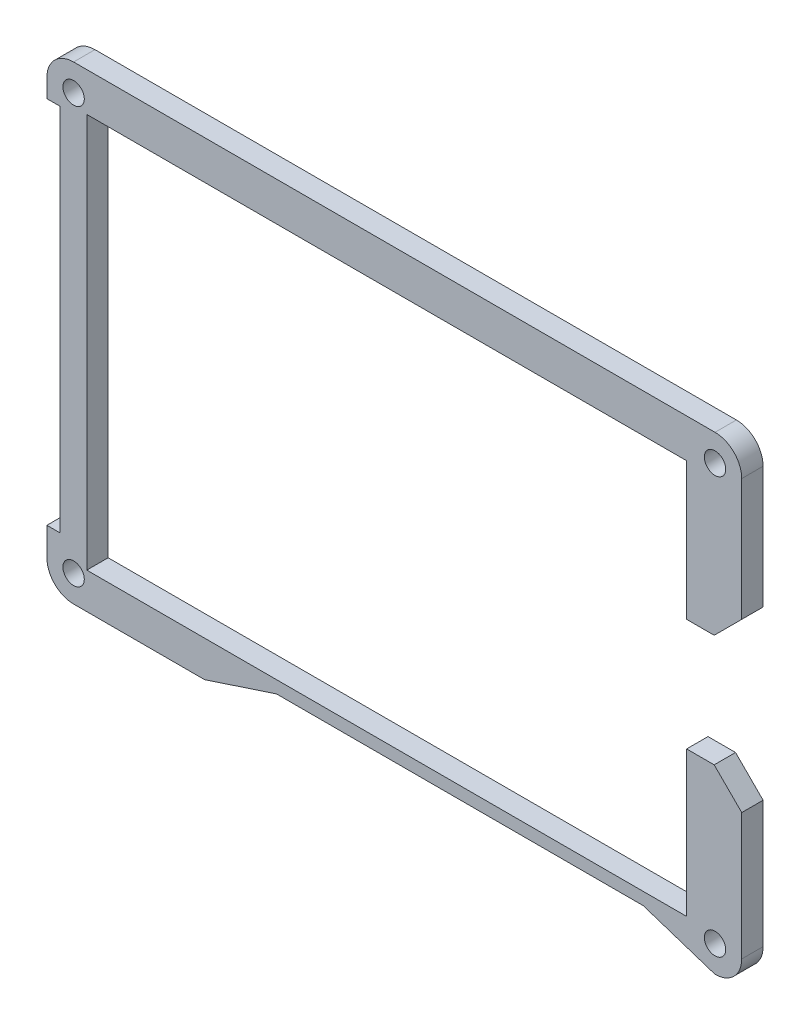
SolidWorks part; units mm, degrees
ref_plane "Front Plane" through (0, 0, 0) normal (0, 0, 1) x (1, 0, 0)
ref_plane "Top Plane" through (0, 0, 0) normal (0, 1, 0) x (1, 0, 0)
ref_plane "Right Plane" through (0, 0, 0) normal (1, 0, 0) x (0, 0, -1)
sketch "Sketch1" plane through (0, 0, 0) normal (0, 0, 1) x (1, 0, 0)
  line L0 (-401.0571, 148.341) -> (-380.1672, 148.341)
  line L1 (-399.1521, 148.341) -> (-399.1521, 95.6449)
  line L2 (-395.3675, 92.9525) -> (-395.3675, 149.2432)
  line L3 (-395.3675, 149.2432) -> (-309.8086, 149.2432)
  line L4 (-395.3675, 92.9525) -> (-309.8086, 92.9525)
  line L5 (-309.8086, 149.2432) -> (-309.8086, 92.9525)
  line L6 (-309.8086, 128.8851) -> (-321.2743, 128.8851)
  line L7 (-321.2743, 128.8851) -> (-321.2743, 115.6771)
  line L8 (-321.2743, 115.6771) -> (-309.8086, 115.6771)
  line L9 (-309.8086, 128.8851) -> (-305.8779, 128.8851)
  line L10 (-375.4172, 95.6449) -> (-401.0571, 95.6449)
  line L11 (-401.0571, 150.9566) -> (-401.0571, 148.341) construction
  line L12 (-305.7573, 154.7804) -> (-397.2471, 154.7804) construction
  line L13 (-301.9473, 91.6317) -> (-301.9473, 150.9704) construction
  line L14 (-315.9973, 91.1883) -> (-305.7573, 87.8217) construction
  line L15 (-315.9973, 91.1883) -> (-368.3165, 91.1883) construction
  line L16 (-368.3165, 91.1883) -> (-378.5565, 87.8217) construction
  line L17 (-378.5565, 87.8217) -> (-397.2472, 87.8217) construction
  line L18 (-401.0571, 95.6449) -> (-401.0571, 91.6593) construction
  line L19 (-401.0571, 150.9566) -> (-401.0571, 148.341)
  line L20 (-305.7573, 154.7804) -> (-397.2471, 154.7804)
  line L21 (-301.9473, 91.6317) -> (-301.9473, 150.9704)
  line L22 (-315.9973, 91.1883) -> (-305.7573, 87.8217)
  line L23 (-315.9973, 91.1883) -> (-368.3165, 91.1883)
  line L24 (-368.3165, 91.1883) -> (-378.5565, 87.8217)
  line L25 (-378.5565, 87.8217) -> (-397.2472, 87.8217)
  line L26 (-401.0571, 95.6449) -> (-401.0571, 91.6593)
  line L27 (-305.8779, 128.8851) -> (-301.9473, 132.8158)
  line L28 (-309.8086, 115.6771) -> (-305.8779, 115.6771)
  line L29 (-305.8779, 115.6771) -> (-301.9473, 111.7464)
  line L30 (-309.8086, 141.4927) -> (-301.9473, 141.4927) construction
  line L31 (-305.878, 141.4927) -> (-305.8779, 128.8851) construction
  arc A0 (-397.2471, 154.7804) -> (-401.0571, 150.9566) centre (-397.2471, 150.9704) ccw construction
  arc A1 (-301.9473, 150.9704) -> (-305.7573, 154.7804) centre (-305.7573, 150.9704) ccw construction
  arc A2 (-305.7573, 87.8217) -> (-301.9473, 91.6317) centre (-305.7573, 91.6317) ccw construction
  arc A3 (-401.0571, 91.6593) -> (-397.2472, 87.8217) centre (-397.2472, 91.6317) ccw construction
  arc A4 (-397.2471, 154.7804) -> (-401.0571, 150.9566) centre (-397.2471, 150.9704) ccw
  arc A5 (-301.9473, 150.9704) -> (-305.7573, 154.7804) centre (-305.7573, 150.9704) ccw
  arc A6 (-305.7573, 87.8217) -> (-301.9473, 91.6317) centre (-305.7573, 91.6317) ccw
  arc A7 (-401.0571, 91.6593) -> (-397.2472, 87.8217) centre (-397.2472, 91.6317) ccw
  circle A8 centre (-397.2471, 150.9704) radius 1.3462 construction
  circle A9 centre (-305.7573, 150.9704) radius 1.3462 construction
  circle A10 centre (-305.7573, 91.6317) radius 1.3462 construction
  circle A11 centre (-397.2472, 91.6317) radius 1.3462 construction
  circle A12 centre (-397.2471, 150.9704) radius 1.3462
  circle A13 centre (-305.7573, 150.9704) radius 1.3462
  circle A14 centre (-305.7573, 91.6317) radius 1.3462
  circle A15 centre (-397.2472, 91.6317) radius 1.3462
  dimension "D1" = 1.905
  dimension "D2" = 5.6896
  dimension "D3" = 5.5372
  dimension "D4" = 5.1308
  dimension "D5" = 7.8613
  dimension "D6" = 25.8953
  dimension "D7" = 13.208
  dimension "D8" = 11.4657
  dimension "D9" = 45
  dimension "D10" = 45
extrude "Boss-Extrude1" add sketch "Sketch1" along normal blind 3.048 contours L21 A5 L20 A4 L19 L0 L2 L3 L5 L9 L27 A13 A12 | L10 L2 L0 L1 | L26 A7 L25 L24 L23 L22 A6 L21 L29 L28 L5 L4 L2 L10 A15 A14
sketch "Sketch2" plane through (0, 0, 0) normal (0, 0, -1) x (-1, 0, 0)
  circle A0 centre (305.7573, 150.9704) radius 1.524
  circle A1 centre (305.7573, 91.6317) radius 1.524
  circle A2 centre (397.2472, 91.6317) radius 1.524
  circle A3 centre (397.2471, 150.9704) radius 1.524
  dimension "D1" = 3.048
extrude "Cut-Extrude1" cut sketch "Sketch2" against normal through all
sketch "Sketch3" plane through (0, 0, 3.048) normal (0, 0, 1) x (1, 0, 0)
  line L0 (-309.8086, 128.8851) -> (-305.8779, 128.8851) construction
  line L1 (-305.8779, 128.8851) -> (-301.9473, 132.8157) construction
  line L2 (-309.8086, 115.6771) -> (-305.8779, 115.6771) construction
  line L3 (-305.8779, 115.6771) -> (-301.9473, 111.7465) construction
  line L4 (-309.8086, 128.8851) -> (-305.8779, 128.8851)
  line L5 (-305.8779, 128.8851) -> (-301.9473, 132.8157)
  line L6 (-309.8086, 115.6771) -> (-305.8779, 115.6771)
  line L7 (-305.8779, 115.6771) -> (-301.9473, 111.7465)
  line L8 (-309.8086, 129.6471) -> (-305.8779, 129.6471)
  line L9 (-309.8086, 149.2432) -> (-309.8086, 128.8851) construction
  line L10 (-305.8779, 129.6471) -> (-301.9473, 133.5777)
  line L11 (-301.9473, 132.8157) -> (-301.9473, 150.9704) construction
  line L12 (-309.8086, 129.6471) -> (-309.8086, 128.8851)
  line L13 (-301.9473, 133.5777) -> (-301.9473, 132.8157)
  line L14 (-309.8086, 115.6771) -> (-309.8086, 113.6451)
  line L15 (-309.8086, 115.6771) -> (-309.8086, 92.9525) construction
  line L16 (-309.8086, 113.6451) -> (-305.8779, 113.6451)
  line L17 (-305.8779, 113.6451) -> (-301.9473, 109.7145)
  line L18 (-301.9473, 91.6317) -> (-301.9473, 111.7465) construction
  line L19 (-301.9473, 109.7145) -> (-301.9473, 111.7465)
  line L20 (-301.9473, 133.5777) -> (-301.9473, 132.8157)
  line L21 (-301.9473, 111.7465) -> (-301.9473, 109.7145)
  line M5 (-301.9473, 132.8157) -> (-301.9473, 150.9704)
  line M20 (-301.9473, 91.6317) -> (-301.9473, 111.7465)
  line M21 (-301.9473, 111.7465) -> (-305.8779, 115.6771)
  line M22 (-305.8779, 115.6771) -> (-309.8086, 115.6771)
  line M23 (-309.8086, 115.6771) -> (-309.8086, 92.9525)
  line M27 (-309.8086, 149.2432) -> (-309.8086, 128.8851)
  line M28 (-309.8086, 128.8851) -> (-305.8779, 128.8851)
  line M29 (-305.8779, 128.8851) -> (-301.9473, 132.8157)
  dimension "D1" = 15.24
  dimension "D2" = 13.97
extrude "Cut-Extrude2" cut sketch "Sketch3" against normal through all contours L10 L8 M27 M28 M29 M5 | L16 L17 M20 M21 M22 M23
